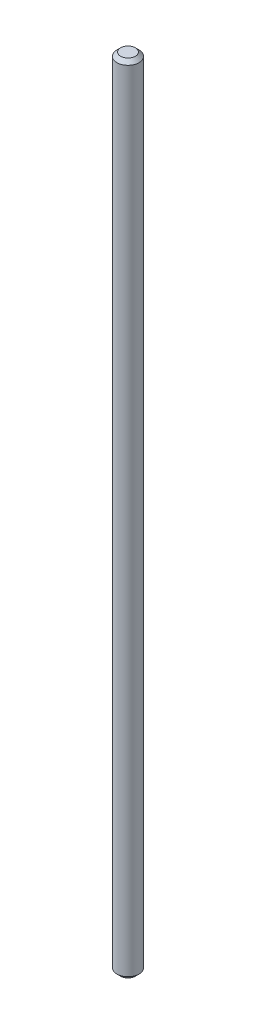
SolidWorks part; units mm, degrees
material "Acero inoxidable al cromo"
ref_plane "Front" through (0, 0, 0) normal (0, 0, 1) x (1, 0, 0)
ref_plane "Top" through (0, 0, 0) normal (0, 1, 0) x (1, 0, 0)
ref_plane "Right" through (0, 0, 0) normal (1, 0, 0) x (0, 0, -1)
sketch "Croquis1" plane through (0, 0, 0) normal (0, 1, 0) x (1, 0, 0)
  circle A0 centre (0, 0) radius 1.5
  dimension "D1" = 3
extrude "Saliente-Extruir1" add sketch "Croquis1" along normal blind 108
chamfer "Chaflán1" distance 0.5 angle 45 2 edges at (0, 108, 1.5) (0, 0, 1.5)
